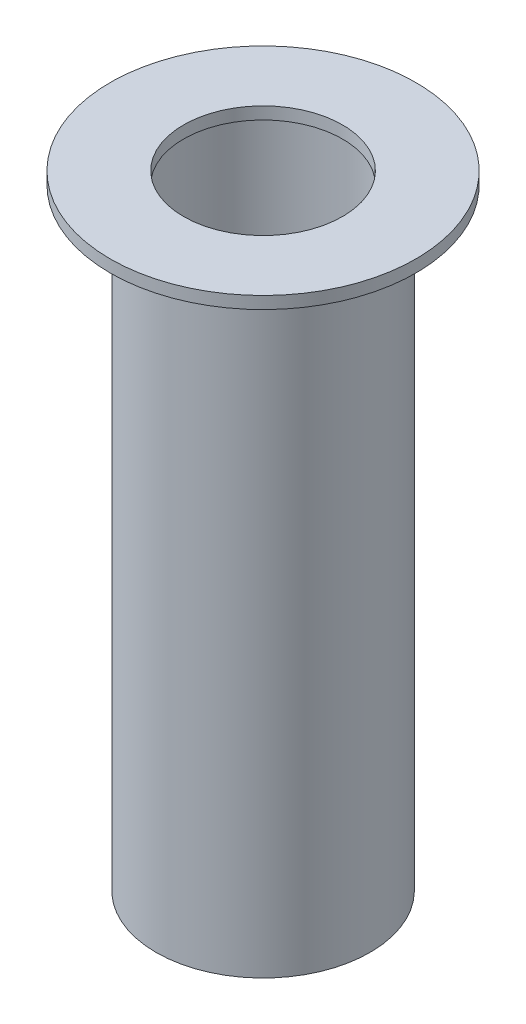
SolidWorks part; units mm, degrees
ref_plane "Front Plane" through (0, 0, 0) normal (0, 0, 1) x (1, 0, 0)
ref_plane "Top Plane" through (0, 0, 0) normal (0, 1, 0) x (1, 0, 0)
ref_plane "Right Plane" through (0, 0, 0) normal (1, 0, 0) x (0, 0, -1)
sketch "Sketch1" plane through (0, 0, 0) normal (0, 1, 0) x (1, 0, 0)
  circle A0 centre (0, 0) radius 6.2
  circle A2 centre (0, 0) radius 7
  dimension "D1" = 12.4
  dimension "D2" = 0.8
extrude "Boss-Extrude1" add sketch "Sketch1" along normal mid plane 40
sketch "Sketch4" plane through (0, 20, 0) normal (0, 1, 0) x (1, 0, 0)
  circle A0 centre (0, 0) radius 5.2
  circle A1 centre (0, 0) radius 10
  dimension "D1" = 20
extrude "Boss-Extrude3" add sketch "Sketch4" along normal blind 0.8
